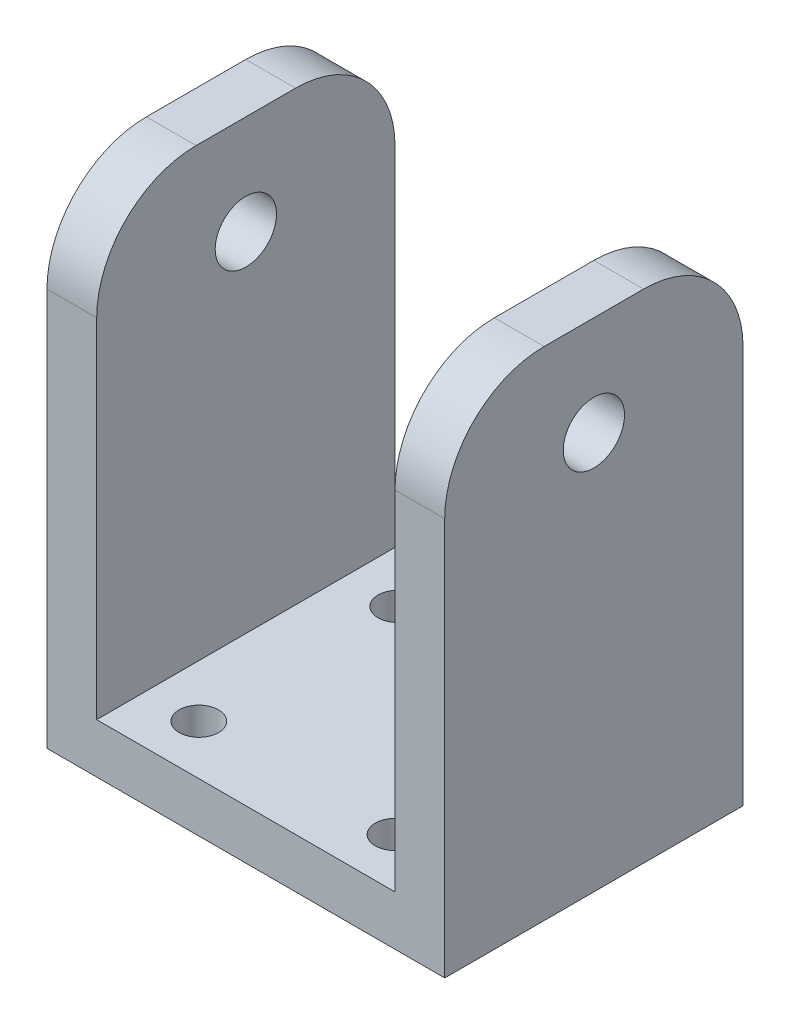
SolidWorks part; units mm, degrees
material "6061 Alloy"
ref_plane "Front Plane" through (0, 0, 0) normal (0, 0, 1) x (1, 0, 0)
ref_plane "Top Plane" through (0, 0, 0) normal (0, 1, 0) x (1, 0, 0)
ref_plane "Right Plane" through (0, 0, 0) normal (1, 0, 0) x (0, 0, -1)
sketch "Sketch1" plane through (0, 0, 0) normal (0, 1, 0) x (1, 0, 0)
  line L1 (0, 0) -> (40, 0)
  line L2 (0, 0) -> (0, 30)
  line L3 (0, 30) -> (40, 30)
  line L4 (40, 0) -> (40, 30)
  dimension "D1" = 30
  dimension "D2" = 40
extrude "Boss-Extrude1" add sketch "Sketch1" along normal blind 50
sketch "Sketch2" plane through (0, 0, 0) normal (0, 0, 1) x (1, 0, 0)
  line L0 (0, 50) -> (40, 50) construction
  line L1 (5, 50) -> (35, 50)
  line L2 (5, 50) -> (5, 5)
  line L3 (5, 5) -> (35, 5)
  line L4 (35, 50) -> (35, 5)
  line L5 (0, 0) -> (40, 0) construction
  line L6 (40, 50) -> (40, 0) construction
  line L7 (0, 50) -> (0, 0) construction
  dimension "D1" = 5
  dimension "D2" = 5
  dimension "D3" = 5
extrude "Cut-Extrude1" cut sketch "Sketch2" against normal blind 30
fillet "Fillet1" radius 10 4 edges at (2.5, 50, -30) (37.5, 50, -30) (37.5, 50, 0) (2.5, 50, 0)
sketch "Sketch3" plane through (0, 5, 0) normal (0, 1, 0) x (1, 0, 0)
  line L0 (5, 0) -> (35, 0) construction
  line L1 (5, 30) -> (35, 30) construction
  circle A0 centre (10.2728, 5) radius 1.9844
  circle A1 centre (10.2728, 25) radius 1.9844
  dimension "D1" = 3.9688
  dimension "D2" = 3.9688
  dimension "D3" = 5
  dimension "D4" = 5
extrude "Cut-Extrude2" cut sketch "Sketch3" against normal blind 30
sketch "Sketch4" plane through (40, 0, 0) normal (1, 0, 0) x (0, 0, -1)
  line L0 (0, 40) -> (0, 0) construction
  line L1 (10, 50) -> (20, 50) construction
  circle A0 centre (15, 40) radius 3.0831
  dimension "D1" = 15
  dimension "D2" = 10
extrude "Cut-Extrude3" cut sketch "Sketch4" against normal blind 55
sketch "Sketch5" plane through (0, 5, 0) normal (0, 1, 0) x (1, 0, 0)
  line L0 (5, 0) -> (35, 0) construction
  line L1 (35, 30) -> (35, 0) construction
  line L2 (5, 30) -> (35, 30) construction
  circle A0 centre (30, 25) radius 1.9844
  circle A1 centre (30, 5) radius 1.9844
  dimension "D1" = 3.9688
  dimension "D2" = 3.9688
  dimension "D3" = 5
  dimension "D4" = 5
  dimension "D5" = 5
  dimension "D6" = 5
extrude "Cut-Extrude4" cut sketch "Sketch5" against normal blind 30
